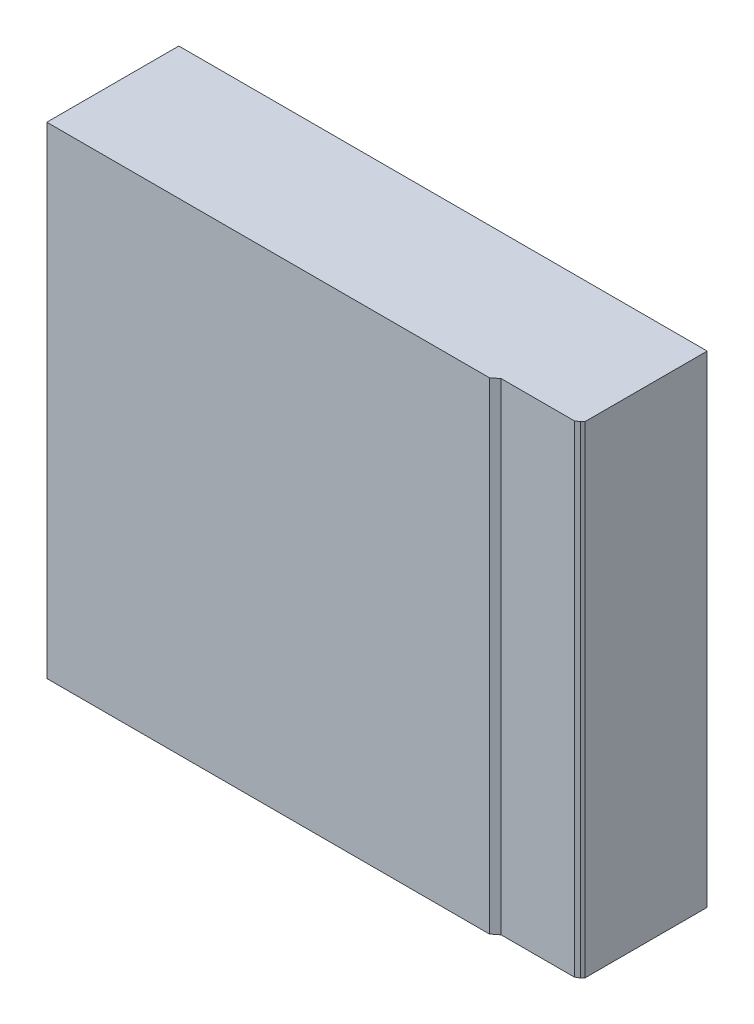
SolidWorks part; units mm, degrees
ref_plane "Спереди" through (0, 0, 0) normal (0, 0, 1) x (1, 0, 0)
ref_plane "Сверху" through (0, 0, 0) normal (0, 1, 0) x (1, 0, 0)
ref_plane "Справа" through (0, 0, 0) normal (1, 0, 0) x (0, 0, -1)
sketch "Эскиз1" plane through (0, 0, 0) normal (0, 1, 0) x (1, 0, 0)
  line L0 (0, 0) -> (670.6326, 0)
  line L1 (670.6326, 0) -> (680.6326, 7.8102)
  line L2 (791.427, 7.8102) -> (797.2885, 11.2996)
  line L3 (791.427, 7.8102) -> (680.6326, 7.8102)
  line L4 (0, 200) -> (800.6326, 200)
  line L5 (797.2885, 11.2996) -> (800.6326, 15)
  line L8 (0, 200) -> (0, 0)
  line L9 (800.6326, 200) -> (800.6326, 15)
extrude "Бобышка-Вытянуть1" add sketch "Эскиз1" along normal blind 730
